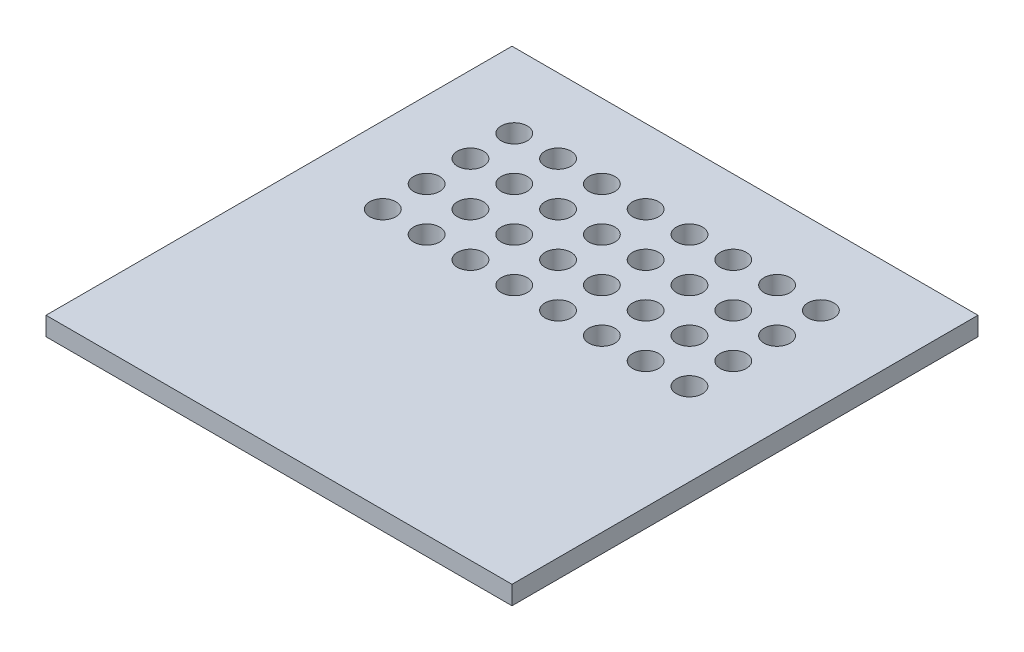
SolidWorks part; units mm, degrees
ref_plane "Front Plane" through (0, 0, 0) normal (0, 0, 1) x (1, 0, 0)
ref_plane "Top Plane" through (0, 0, 0) normal (0, 1, 0) x (1, 0, 0)
ref_plane "Right Plane" through (0, 0, 0) normal (1, 0, 0) x (0, 0, -1)
sketch "Sketch1" plane through (0, 0, 0) normal (0, 1, 0) x (1, 0, 0)
  line L1 (-12.5, 12.5) -> (12.5, 12.5)
  line L2 (-12.5, 12.5) -> (-12.5, -12.5)
  line L3 (-12.5, -12.5) -> (12.5, -12.5)
  line L4 (12.5, 12.5) -> (12.5, -12.5)
  circle A0 centre (-8.39, 8.51) radius 0.7
  circle A1 centre (-6.04, 8.51) radius 0.7
  circle A2 centre (-3.69, 8.51) radius 0.7
  circle A3 centre (-1.34, 8.51) radius 0.7
  circle A4 centre (1.01, 8.51) radius 0.7
  circle A5 centre (3.36, 8.51) radius 0.7
  circle A6 centre (5.71, 8.51) radius 0.7
  circle A7 centre (8.06, 8.51) radius 0.7
  circle A8 centre (-6.04, 6.16) radius 0.7
  circle A9 centre (-3.69, 6.16) radius 0.7
  circle A10 centre (-1.34, 6.16) radius 0.7
  circle A11 centre (1.01, 6.16) radius 0.7
  circle A12 centre (3.36, 6.16) radius 0.7
  circle A13 centre (5.71, 6.16) radius 0.7
  circle A14 centre (8.06, 6.16) radius 0.7
  circle A15 centre (-6.04, 3.81) radius 0.7
  circle A16 centre (-3.69, 3.81) radius 0.7
  circle A17 centre (-1.34, 3.81) radius 0.7
  circle A18 centre (1.01, 3.81) radius 0.7
  circle A19 centre (3.36, 3.81) radius 0.7
  circle A20 centre (5.71, 3.81) radius 0.7
  circle A21 centre (8.06, 3.81) radius 0.7
  circle A22 centre (-6.04, 1.46) radius 0.7
  circle A23 centre (-3.69, 1.46) radius 0.7
  circle A24 centre (-1.34, 1.46) radius 0.7
  circle A25 centre (1.01, 1.46) radius 0.7
  circle A26 centre (3.36, 1.46) radius 0.7
  circle A27 centre (5.71, 1.46) radius 0.7
  circle A28 centre (8.06, 1.46) radius 0.7
  circle A29 centre (-8.39, 6.16) radius 0.7
  circle A30 centre (-8.39, 3.81) radius 0.7
  circle A31 centre (-8.39, 1.46) radius 0.7
  dimension "D5" = 8
  dimension "D7" = 3.99
  dimension "D1" = 12.5
  dimension "D2" = 25
  dimension "D3" = 12.5
  dimension "D4" = 25
  dimension "D8" = 4.11
  dimension "D6" = 4
extrude "Boss-Extrude1" add sketch "Sketch1" along normal blind 1
